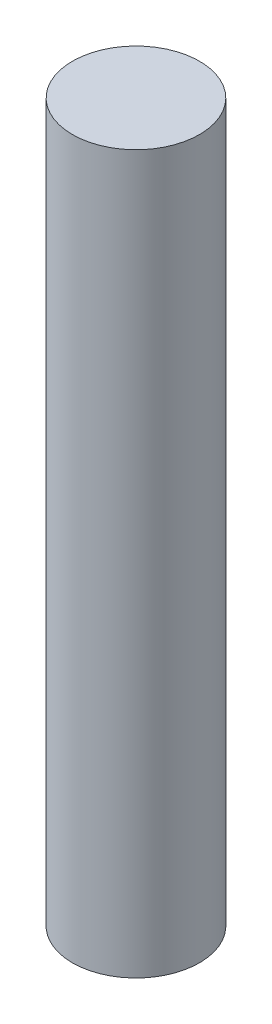
SolidWorks part; units mm, degrees
ref_plane "Alzado" through (0, 0, 0) normal (0, 0, 1) x (1, 0, 0)
ref_plane "Planta" through (0, 0, 0) normal (0, 1, 0) x (1, 0, 0)
ref_plane "Vista lateral" through (0, 0, 0) normal (1, 0, 0) x (0, 0, -1)
sketch "Croquis1" plane through (0, 0, 0) normal (0, 1, 0) x (1, 0, 0)
  circle A0 centre (0, 0) radius 22.5
  dimension "D1" = 45
extrude "Saliente-Extruir1" add sketch "Croquis1" along normal blind 254
